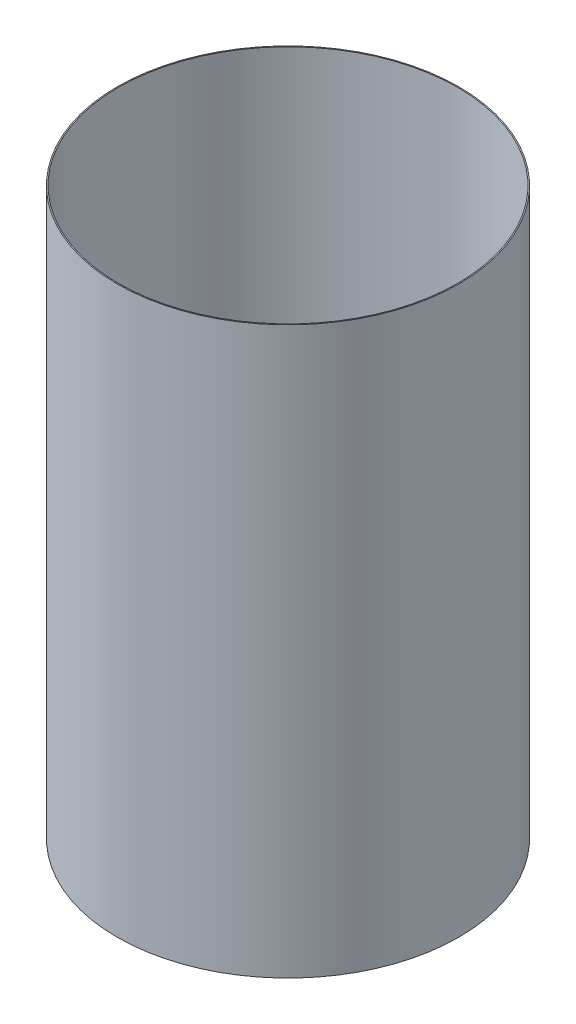
SolidWorks part; units mm, degrees
material "Thornel Mat VMA"
ref_plane "Front Plane" through (0, 0, 0) normal (0, 0, 1) x (1, 0, 0)
ref_plane "Top Plane" through (0, 0, 0) normal (0, 1, 0) x (1, 0, 0)
ref_plane "Right Plane" through (0, 0, 0) normal (1, 0, 0) x (0, 0, -1)
ref_axis "Axis1" through (0, 55, 0) along (0, -1, 0)
sketch "Sketch1" plane through (0, 0, 0) normal (0, 0, 1) x (1, 0, 0)
  line L0 (-40.005, -69.0032) -> (-40.005, -202.3532)
  line L2 (-38.1, -202.3532) -> (0, -202.3532) construction
  line L3 (-38.1, -69.0032) -> (0, -69.0032) construction
revolve "Revolve-Thin1" add sketch "Sketch1" angle 360 about axis through (0, 55, 0) along (0, -1, 0)
equation "\"D3@Revolve-Thin1\"=\"CF THICKNESS@Cryo Tank.SLDASM\""
